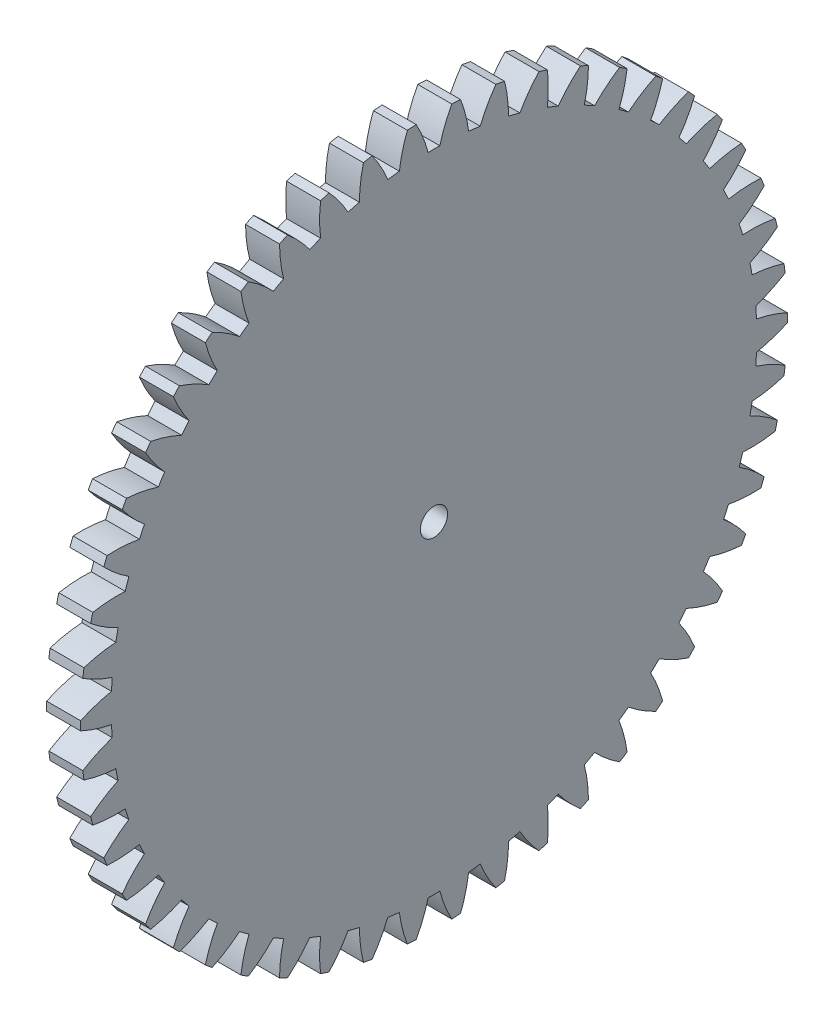
SolidWorks part; units mm, degrees
ref_plane "Plane1" through (0, 0, 0) normal (0, 0, 1) x (1, 0, 0)
ref_plane "Plane2" through (0, 0, 0) normal (0, 1, 0) x (1, 0, 0)
ref_plane "Plane3" through (0, 0, 0) normal (1, 0, 0) x (0, 0, -1)
sketch "HoldingSke" plane through (0, 0, 0) normal (0, 1, 0) x (1, 0, 0)
  line L0 (0, 0) -> (0.3214, -0.383)
  line L1 (-15, 0) -> (100, 0) construction
  line L2 (0, 0) -> (-2.1039, 2.3779)
  line L3 (0, 0) -> (-11.863, 4.5341)
  line L4 (0, 0) -> (5.5511, 6.6156)
  line L5 (0, 0) -> (-18.7391, -6.9891)
  line L6 (0, 0) -> (-8.2896, -5.593)
  line L7 (-2.1039, 2.3779) -> (2.2011, 21.9091)
  line L8 (-76.2, 54.61) -> (-75.5, 54.61)
  line L9 (-71.009, 38.7566) -> (-53.1078, 45.2721)
  line L10 (-76.2, 71.12) -> (104.1128, 71.12)
  line L11 (0, 0) -> (-10, 0)
  line L12 (-76.2, 101.6) -> (-76.133, 101.6)
  line L13 (24.9733, 27.94) -> (52.9518, 28.4284)
  line L14 (24.9733, 27.94) -> (24.9743, 27.94)
  line L15 (24.9733, 27.94) -> (100.4006, 29.5858)
  line L16 (-63.627, -2) -> (-12.827, -2)
  circle A0 centre (0, 0) radius 2
  circle A1 centre (0, 0) radius 25
  circle A2 centre (0, 0) radius 25
  circle A3 centre (0, 0) radius 2
  dimension "MHD" = 50
  dimension "Hub_dia" = 50
  dimension "Bore" = 4
  dimension "MBD" = 4
  dimension "Num_teeth" = 50
  dimension "Pitch_radius" = 180.3128
  dimension "Pitch" = 0.5
  dimension "Width" = 10
  dimension "Overall_len" = 20
  dimension "Show_teeth" = 50
  dimension "Thickness" = 10
  dimension "OAL" = 20.0001
  dimension "T_dim" = 0.7
  dimension "Ap" = 20
  dimension "H" = 19.05
  dimension "Backlash" = 0.067
  dimension "Addendum_fac" = 1
  dimension "Dedendum_fac" = 1.25
  dimension "Clearance_fac" = 0.25
  dimension "Dedendum_add" = 0.001
  dimension "Module" = 2
sketch "BasProSke" plane through (0, 0, 0) normal (0, 1, 0) x (1, 0, 0)
  line L0 (-10, 0) -> (60, 0) construction
  line L1 (0, 0) -> (0, 52)
  line L2 (0, 0) -> (10, 0)
  line L3 (10, 0) -> (10, 52)
  line L4 (10, 52) -> (0, 52)
  dimension "Diameter" = 104
  dimension "Thickness" = 10
revolve "Base-Revolve" add sketch "BasProSke" angle 360 about L0
sketch "TooCutSke" plane through (0, 0, 0) normal (1, 0, 0) x (0, 0, -1)
  line L1 (0, 0) -> (0, 107) construction
  line L2 (0, 0) -> (-1.6878, 49.9715) construction
  line L3 (0, 0) -> (-6.2764, 99.7605) construction
  line L4 (-1.6878, 49.9715) -> (-3.1382, 49.8803) construction
  arc A0 (0.8606, 47.4912) -> (-0.8606, 47.4912) centre (0, 0) ccw
  arc A1 (2.629, 51.9589) -> (-2.629, 51.9589) centre (0, 0) ccw
  circle A2 centre (0, 0) radius 50 construction
  circle A3 centre (0, 0) radius 46.9846 construction
  arc A4 (-0.8606, 47.4912) -> (-2.629, 51.9589) centre (-20.2064, 42.4176) ccw
  arc A5 (2.629, 51.9589) -> (0.8606, 47.4912) centre (20.2064, 42.4176) ccw
  dimension "Root_dia" = 94.998
  dimension "Overcut_dia" = 104.0508
  dimension "Pitch_dia" = 100
  dimension "Base_dia" = 93.9693
  dimension "Flank_rad" = 20
  dimension "Half_ang" = 3.6
  dimension "Half_CT" = 1.4533
extrude "ToothCut" cut sketch "TooCutSke" along normal through all
fillet "Breaks" [suppressed] radius 0.04
fillet "RootFillets" [suppressed] radius 0.501
pattern_circular "TeethCuts" count 50 every 7.2 about axis through (-10, 0, 0) along (1, 0, 0) of "ToothCut", "RootFillets", "Breaks"
sketch "HubNeaOneSke" plane through (0, 0, 0) normal (-1, 0, 0) x (0, 0, 1)
  circle A0 centre (0, 0) radius 25
  dimension "Diameter" = 50
extrude "HubNearOne" add sketch "HubNeaOneSke" along normal blind 10.0001
sketch "HubNeaBotSke" plane through (0, 0, 0) normal (-1, 0, 0) x (0, 0, 1)
  circle A0 centre (0, 0) radius 25
  dimension "Diameter" = 50
extrude "HubNearBoth" [suppressed] add sketch "HubNeaBotSke" along normal blind 5
ref_plane "FarPln" through (10, 0, 0) normal (1, 0, 0) x (0, 0, -1)
sketch "HubFarSke" plane through (10, 0, 0) normal (1, 0, 0) x (0, 0, -1)
  circle A0 centre (0, 0) radius 25
  dimension "Diameter" = 50
extrude "HubFar" [suppressed] add sketch "HubFarSke" along normal blind 5
sketch "BorSke" plane through (0, 0, 0) normal (1, 0, 0) x (0, 0, -1)
  circle A0 centre (0, 0) radius 2
  dimension "Diameter" = 4
extrude "Bore" cut sketch "BorSke" along normal mid plane 40.0001
sketch "KeySke" plane through (0, 0, 0) normal (1, 0, 0) x (0, 0, -1)
  line L0 (-0.8, 0) -> (-0.8, 2.7)
  line L1 (-0.8, 2.7) -> (0.8, 2.7)
  line L2 (0.8, 2.7) -> (0.8, 0)
  line L3 (0, 0) -> (0, 34) construction
  line L4 (-0.8, 0) -> (0.8, 0)
  dimension "Offset" = 2.7
  dimension "Width" = 1.6
extrude "Keyway" [suppressed] cut sketch "KeySke" along normal mid plane 40.0001
pattern_circular "Keyway2" [suppressed] count 2 every 90 about axis through (-10, 0, 0) along (1, 0, 0)
sketch "Esquisse1" plane through (-10.0001, 0, 0) normal (-1, 0, 0) x (0, 0, 1)
  circle A0 centre (0, 0) radius 25
  dimension "D1" = 50
extrude "Enlèv. mat.-Extru.1" cut sketch "Esquisse1" against normal blind 5
sketch "Esquisse2" plane through (10, 0, 0) normal (1, 0, 0) x (0, 0, -1)
  circle A0 centre (0, 0) radius 52
  dimension "D1" = 104
extrude "Enlèv. mat.-Extru.2" cut sketch "Esquisse2" against normal blind 5
equation "' \"Module@HoldingSke\" = 6.35"
equation "' \"Num_teeth@HoldingSke\" = 12"
equation "' \"Ap@HoldingSke\" =  20"
equation "' \"Width@HoldingSke\" = 0.5 * 25.4"
equation "' \"Hub_dia@HoldingSke\"= 1 * 25.4"
equation "' \"Overall_len@HoldingSke\" = 1.0 * 25.4"
equation "' \"Bore@HoldingSke\" = 0.75 * 25.4"
equation "' \"T_dim@HoldingSke\" = 0.1 * 25.4"
equation "' \"Width@KeySke\" = 0.25 * 25.4"
equation "' \"Show_teeth@HoldingSke\" = 13"
equation "' \"Backlash@HoldingSke\" = 0.009 * 25.4"
equation "' \"Addendum_fac@HoldingSke\" = 1.0"
equation "' \"Dedendum_fac@HoldingSke\" = 1.25"
equation "' \"Dedendum_add@HoldingSke\" = 0.00005 * 25.4"
equation "' \"Clearance_fac@HoldingSke\" = 0.25"
equation "\"Pitch@HoldingSke\" = 1 / \"Module@HoldingSke\""
equation "\"Overcut_dia@TooCutSke\" = (\"Num_teeth@HoldingSke\" + 2 * \"Addendum_fac@HoldingSke\") / \"Pitch@HoldingSke\" + 0.002 * 25.4"
equation "\"Pitch_dia@TooCutSke\" = \"Num_teeth@HoldingSke\" / \"Pitch@HoldingSke\""
equation "\"Base_dia@TooCutSke\" = \"Num_teeth@HoldingSke\" / \"Pitch@HoldingSke\" * cos((\"Ap@HoldingSke\"  * 3.14159265 / 180))"
equation "\"Root_dia@TooCutSke\" = (\"Num_teeth@HoldingSke\" + 2) / \"Pitch@HoldingSke\" - 2 * (\"Addendum_fac@HoldingSke\" + \"Dedendum_fac@HoldingSke\") / \"Pitch@HoldingSke\" - \"Dedendum_add@HoldingSke\" * 2"
equation "\"Half_ang@TooCutSke\" = 180 / \"Num_teeth@HoldingSke\""
equation "\"Half_CT@TooCutSke\" = \"Num_teeth@HoldingSke\" / \"Pitch@HoldingSke\" * sin((3.14159265 / 2 / \"Num_teeth@HoldingSke\")) / 2 - 7 * \"Backlash@HoldingSke\" / 4"
equation "\"Flank_rad@TooCutSke\" = \"Num_teeth@HoldingSke\" / \"Pitch@HoldingSke\" / 5"
equation "\"Radius@RootFillets\" = \"Clearance_fac@HoldingSke\" / \"Pitch@HoldingSke\" + \"Dedendum_add@HoldingSke\""
equation "\"Break_rad@Breaks\" = 0.02 / \"Pitch@HoldingSke\""
equation "\"Thickness@HoldingSke\" = \"Width@HoldingSke\""
equation "\"OAL@HoldingSke\" = \"Thickness@HoldingSke\""
equation "\"MHD@HoldingSke\" = (\"Num_teeth@HoldingSke\" + 2) / \"Pitch@HoldingSke\" - 2 * (\"Addendum_fac@HoldingSke\" + \"Dedendum_fac@HoldingSke\")  / \"Pitch@HoldingSke\" - \"Dedendum_add@HoldingSke\" * 2"
equation "\"MBD@HoldingSke\" = (\"Num_teeth@HoldingSke\" + 2) / \"Pitch@HoldingSke\" - 2 * (\"Addendum_fac@HoldingSke\" + \"Dedendum_fac@HoldingSke\")  / \"Pitch@HoldingSke\" - \"Dedendum_add@HoldingSke\" * 2 - 0.002 * 25.4"
equation "\"MHD@HoldingSke\" = ((sgn( \"MHD@HoldingSke\" - \"Hub_dia@HoldingSke\" )-1)*( \"MHD@HoldingSke\" - \"Hub_dia@HoldingSke\" ))/-2+ \"Hub_dia@HoldingSke\""
equation "\"MBD@HoldingSke\" = ((sgn( \"MBD@HoldingSke\" - \"Bore@HoldingSke\" )-1)*( \"MBD@HoldingSke\" - \"Bore@HoldingSke\" ))/-2+ \"Bore@HoldingSke\""
equation "\"OAL@HoldingSke\" = ((sgn( \"OAL@HoldingSke\" - \"Overall_len@HoldingSke\" )+1)*( \"OAL@HoldingSke\" - \"Overall_len@HoldingSke\" ))/2 + \"Overall_len@HoldingSke\" + 0.000002 * 25.4"
equation "\"Num_teeth@TeethCuts\" = int( \"Show_teeth@HoldingSke\" ) + 1"
equation "\"Num_teeth@TeethCuts\" = ((sgn( \"Num_teeth@TeethCuts\" - \"Num_teeth@HoldingSke\" )-1)*( \"Num_teeth@TeethCuts\" - \"Num_teeth@HoldingSke\" ))/-2+ \"Num_teeth@HoldingSke\""
equation "\"Num_teeth@TeethCuts\" = ((sgn( \"Num_teeth@TeethCuts\" - 2.0)+1)*( \"Num_teeth@TeethCuts\" - 2.0))/2 +2.0"
equation "\"Angle@TeethCuts\" = 360.0 / \"Num_teeth@HoldingSke\""
equation "\"Diameter@BasProSke\" = (\"Num_teeth@HoldingSke\" + 2 * \"Addendum_fac@HoldingSke\") / \"Pitch@HoldingSke\""
equation "\"Thickness@BasProSke\"  = \"Thickness@HoldingSke\""
equation "' \"Fillet_rad@BasProSke\" =  \"Thickness@HoldingSke\" * 0.05"
equation "\"MHD@HoldingSke\" = ((sgn( \"MHD@HoldingSke\" - \"Root_dia@TooCutSke\" )-1)*( \"MHD@HoldingSke\" - \"Root_dia@TooCutSke\" ))/-2+ \"Root_dia@TooCutSke\""
equation "\"Diameter@HubNeaOneSke\" = \"MHD@HoldingSke\""
equation "\"Length@HubNearOne\" = \"OAL@HoldingSke\" - \"Thickness@BasProSke\""
equation "\"Diameter@HubNeaBotSke\" = \"MHD@HoldingSke\""
equation "\"Length@HubNearBoth\" = ( \"OAL@HoldingSke\" - \"Thickness@BasProSke\" ) / 2.0"
equation "\"Thickness@FarPln\" = \"Thickness@BasProSke\""
equation "\"Diameter@HubFarSke\" = \"MHD@HoldingSke\""
equation "\"Length@HubFar\" = ( \"OAL@HoldingSke\" - \"Thickness@BasProSke\" ) / 2.0"
equation "\"Diameter@BorSke\" = \"MBD@HoldingSke\""
equation "\"D1@Bore\" = \"OAL@HoldingSke\" * 2.0"
equation "\"D1@Keyway\" = \"OAL@HoldingSke\" * 2.0"
equation "\"Offset@KeySke\" = \"T_dim@HoldingSke\" + \"MBD@HoldingSke\" / 2.0"
